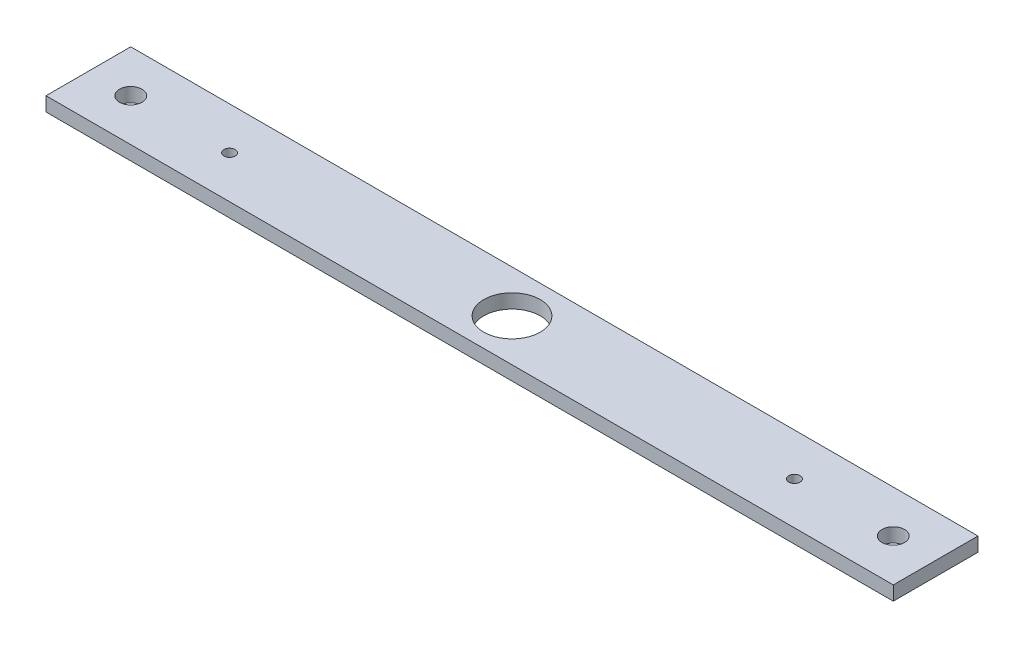
SolidWorks part; units mm, degrees
ref_plane "Front Plane" through (0, 0, 0) normal (0, 0, 1) x (1, 0, 0)
ref_plane "Top Plane" through (0, 0, 0) normal (0, 1, 0) x (1, 0, 0)
ref_plane "Right Plane" through (0, 0, 0) normal (1, 0, 0) x (0, 0, -1)
sketch "Sketch2" plane through (0, 0, 0) normal (0, 1, 0) x (1, 0, 0)
  line L1 (-150, -15) -> (150, -15)
  line L2 (-150, -15) -> (-150, 15)
  line L3 (-150, 15) -> (150, 15)
  line L4 (150, -15) -> (150, 15)
  line L5 (-150, -15) -> (150, 15) construction
  line L6 (-150, 15) -> (150, -15) construction
  point P0 (0, 0)
  dimension "D1" = 300
  dimension "D2" = 30
extrude "Boss-Extrude1" add sketch "Sketch2" along normal blind 5
sketch "Sketch3" plane through (0, 5, 0) normal (0, 1, 0) x (1, 0, 0)
  line L0 (-150, 0) -> (150, 0) construction
  line L1 (-150, 15) -> (-150, -15) construction
  line L2 (150, -15) -> (150, 15) construction
  circle A0 centre (-135, 0) radius 4
  circle A1 centre (0, 0) radius 10
  circle A2 centre (135, 0) radius 4
  dimension "D1" = 8
  dimension "D2" = 20
  dimension "D3" = 15
  dimension "D4" = 15
extrude "Cut-Extrude1" cut sketch "Sketch3" against normal blind 5
sketch "Sketch5" plane through (0, 5, 0) normal (0, 1, 0) x (1, 0, 0)
  line L0 (-150, 0) -> (150, 0) construction
  line L1 (-150, 15) -> (-150, -15) construction
  line L2 (150, -15) -> (150, 15) construction
  circle A0 centre (100, 0) radius 2
  circle A1 centre (-100, 0) radius 2
  point P10 (91.8739, 0)
  dimension "D1" = 4
  dimension "D2" = 4
  dimension "D3" = 50
  dimension "D4" = 50
extrude "Cut-Extrude2" cut sketch "Sketch5" against normal blind 5
